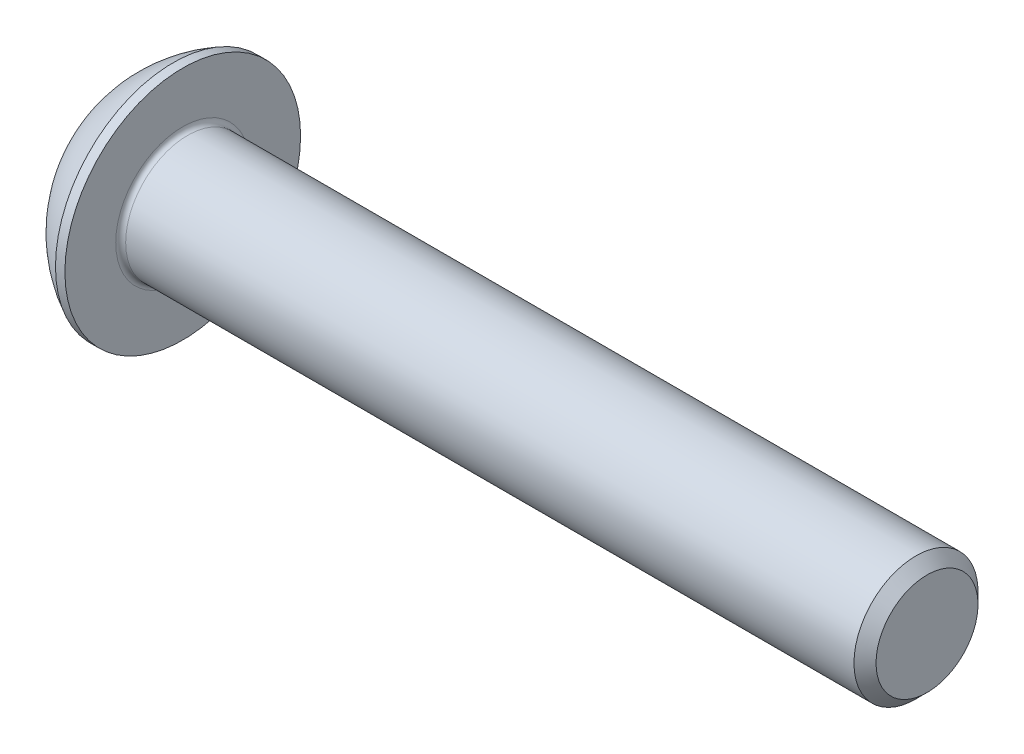
SolidWorks part; units mm, degrees
ref_plane "Plane1" through (0, 0, 0) normal (0, 0, 1) x (1, 0, 0)
ref_plane "Plane2" through (0, 0, 0) normal (0, 1, 0) x (1, 0, 0)
ref_plane "Plane3" through (0, 0, 0) normal (1, 0, 0) x (0, 0, -1)
sketch "BodySke" plane through (0, 0, 0) normal (0, 0, 1) x (1, 0, 0)
  line L0 (32.75, 0) -> (32.75, 2.055)
  line L1 (32.305, 2.5) -> (2.75, 2.5)
  line L2 (2.75, 2.5) -> (2.75, 4.75)
  line L3 (2.75, 4.75) -> (2.37, 4.75)
  line L4 (0, 0) -> (101.6, 0) construction
  line L5 (2.75, -4.75) -> (2.37, -4.75) construction
  line L6 (55.6768, -2.5) -> (2.75, -2.5) construction
  line L7 (32.75, 0) -> (0, 0)
  line L8 (0, 2.375) -> (0, -2.375) construction
  line L9 (0, 0) -> (0, 2.375)
  line L10 (32.75, 2.055) -> (32.305, 2.5)
  line L11 (32.75, -2.055) -> (32.305, -2.5) construction
  line L12 (3.55, 9.525) -> (3.55, -2.5) construction
  line L13 (2.75, 9.525) -> (2.75, -2.5) construction
  arc A1 (0, 2.375) -> (2.37, 4.75) centre (4.755, 0) cw
  dimension "Diameter" = 5
  dimension "Length" = 30
  dimension "Head_dia" = 9.5
  dimension "D1" = 4.75
  dimension "Head_ht" = 2.75
  dimension "Head_side_ht" = 0.38
  dimension "Minor_dia" = 4.11
  dimension "Body_ch_ang" = 45
  dimension "Advance" = 0.8
  dimension "Thread_nom" = 30
revolve "BaseBody" add sketch "BodySke" angle 360 about L4
cosmetic thread "ThreadCosmetic" [suppressed] parameters "Thread_length"=28.4, "Thread_minor"=4.11
fillet "Fillet1" radius 0.2 1 edges at (2.75, 0, 2.5)
sketch "Sketch2" plane through (0, 0, 0) normal (0, 0, 1) x (1, 0, 0)
  line L0 (0, 1.5) -> (1.56, 1.5)
  line L1 (1.56, 1.5) -> (2.426, 0)
  line L3 (2.426, 0) -> (0, 0)
  line L4 (0, 0) -> (0, 1.5)
  line L5 (0, -1.5) -> (1.56, -1.5) construction
  line L6 (0, 0) -> (47.625, 0) construction
  dimension "D2" = 60
  dimension "PreBroach_depth" = 1.56
  dimension "PreBroach_dia" = 3
revolve "PreBroach" cut sketch "Sketch2" angle 360 about L6
sketch "Sketch3" plane through (0, 0, 0) normal (1, 0, 0) x (0, 0, -1)
  line L0 (-1.5, -0.866) -> (-1.5, 0.866)
  line L1 (-1.5, 0.866) -> (0, 1.7321)
  line L2 (0, 1.7321) -> (1.5, 0.866)
  line L3 (1.5, 0.866) -> (1.5, -0.866)
  line L4 (1.5, -0.866) -> (0, -1.7321)
  line L5 (0, -1.7321) -> (-1.5, -0.866)
  dimension "Hex_size" = 3
  dimension "D3" = 3
  dimension "D1" = 1.5
  dimension "D2" = 1.5
extrude "Hex" cut sketch "Sketch3" along normal blind 1.56
sketch "ThdSchSke" plane through (0, 0, 0) normal (0, 0, 1) x (1, 0, 0)
  line L0 (4.35, -2.055) -> (4.0384, -2.5)
  line L1 (4.35, -2.055) -> (4.6616, -2.5)
  line L2 (4.6616, -2.5) -> (4.6616, -3.125)
  line L3 (-3.175, 0) -> (5.1513, 0) construction
  line L5 (4.6616, -3.125) -> (4.0384, -3.125)
  line L6 (4.0384, -3.125) -> (4.0384, -2.5)
  dimension "Diameter" = 5
  dimension "Thread_minor" = 4.11
  dimension "SideAngle" = 55
  dimension "VeeAngle" = 70
  dimension "Overcut" = 6.25
  dimension "Start" = 4.35
revolve "ThreadSchematic" [suppressed] cut sketch "ThdSchSke" angle 360 about L3
pattern_linear "ThdSchPat" [suppressed]
equation "\"D1@BodySke\" = \"Head_dia@BodySke\" * .5"
equation "\"Thread_minor@ThreadCosmetic\" = \"Minor_dia@BodySke\""
equation "\"D1@Sketch3\" = \"Hex_size@Sketch3\" / 2"
equation "\"D2@Sketch3\" = \"D1@Sketch3\""
equation "\"D3@Sketch3\" = \"Hex_size@Sketch3\""
equation "\"Thread_length@ThreadCosmetic\" = ((sgn( (\"Length@BodySke\" - \"Advance@BodySke\" * 2.0) - \"Thread_nom@BodySke\" )-1)*( (\"Length@BodySke\" - \"Advance@BodySke\" * 2.0) - \"Thread_nom@BodySke\" ))/-2+ \"Thread_nom@BodySke\""
equation "\"Thread_minor@ThdSchSke\" = \"Minor_dia@BodySke\""
equation "\"Diameter@ThdSchSke\" = \"Diameter@BodySke\""
equation "\"Overcut@ThdSchSke\" = \"Diameter@BodySke\" * 1.25"
equation "\"Start@ThdSchSke\" = \"Head_ht@BodySke\" + \"Length@BodySke\" - \"Thread_length@ThreadCosmetic\"  '---Non-countersunk---"
equation "\"Num_threads@ThdSchPat\" = int( \"Thread_length@ThreadCosmetic\" / \"Advance@BodySke\" + 0.999 )  + 1"
equation "\"Advance@ThdSchPat\" = \"Thread_length@ThreadCosmetic\" /  (\"Num_threads@ThdSchPat\" - 1) 'relax it"
equation "\"Num_threads@ThdSchPat\" = \"Num_threads@ThdSchPat\" - sgn( \"Num_threads@ThdSchPat\" - 1) '---chamfered tips only---"
